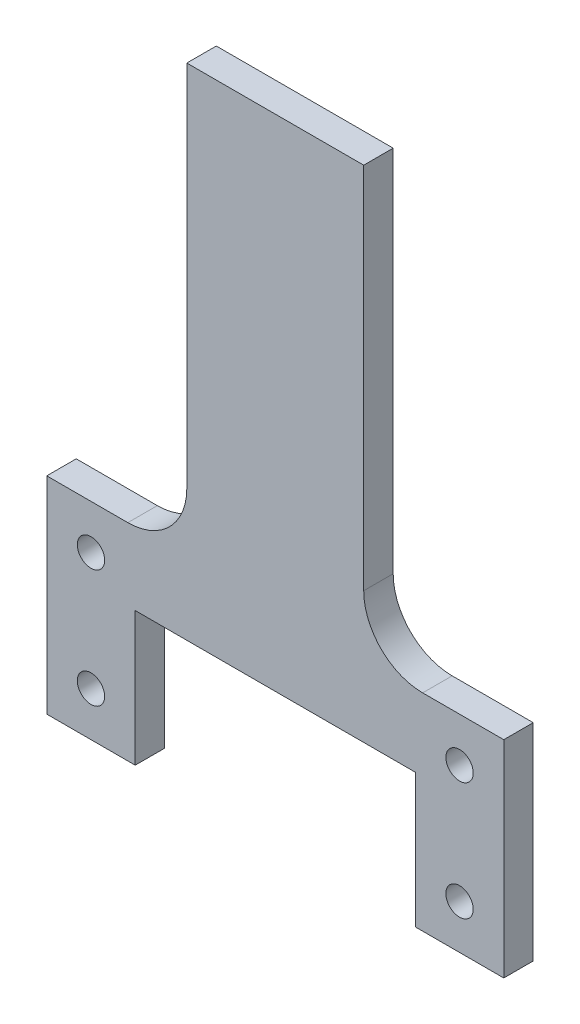
SolidWorks part; units mm, degrees
ref_plane "Front Plane" through (0, 0, 0) normal (0, 0, 1) x (1, 0, 0)
ref_plane "Top Plane" through (0, 0, 0) normal (0, 1, 0) x (1, 0, 0)
ref_plane "Right Plane" through (0, 0, 0) normal (1, 0, 0) x (0, 0, -1)
sketch "Sketch1" plane through (0, 0, 0) normal (0, 0, 1) x (1, 0, 0)
  line L0 (0, 0) -> (0, -21.6729) construction
  line L1 (-15.0812, -10.9093) -> (15.0813, -10.9093) construction
  line L2 (-15.0813, 3.3878) -> (-15.0812, -10.9093) construction
  line L3 (-15.0813, -3.0353) -> (-15.0812, -17.4625)
  line L4 (-15.0812, -17.4625) -> (-24.6062, -17.4625)
  line L5 (-24.6062, -17.4625) -> (-24.6062, 4.7625)
  line L6 (-15.0813, -3.0353) -> (15.0813, -3.0353)
  line L7 (-24.6062, 4.7625) -> (-9.525, 4.7625)
  line L8 (-9.525, 4.7625) -> (-9.525, 50.8)
  line L9 (-9.525, 50.8) -> (9.525, 50.8)
  line L10 (15.0813, 3.3878) -> (15.0813, -10.9093) construction
  line L11 (9.525, 4.7625) -> (9.525, 50.8)
  line L12 (24.6062, 4.7625) -> (9.525, 4.7625)
  line L13 (24.6063, -17.4625) -> (24.6062, 4.7625)
  line L14 (15.0813, -17.4625) -> (24.6063, -17.4625)
  line L15 (15.0813, -3.0353) -> (15.0813, -17.4625)
  circle A0 centre (-19.8438, 0) radius 1.9812 construction
  circle A1 centre (-19.8438, -12.7) radius 1.9812 construction
  circle A2 centre (19.8438, -12.7) radius 1.9812 construction
  circle A3 centre (19.8438, 0) radius 1.9812 construction
  circle A4 centre (19.8438, -12.7) radius 1.9812 construction
  circle A5 centre (19.8438, 0) radius 1.9812 construction
  point P26 (0, -10.9093)
  point P27 (0, 50.8)
  point P30 (0, -3.0353)
  dimension "D1" = 3.9624
  dimension "D2" = 12.7
  dimension "D3" = 39.6875
  dimension "D4" = 10.9093
  dimension "D5" = 4.7625
  dimension "D6" = 7.874
  dimension "D7" = 4.7625
  dimension "D8" = 4.7625
  dimension "D9" = 19.05
  dimension "D10" = 50.8
  dimension "D11" = 4.7625
extrude "Boss-Extrude1" add sketch "Sketch1" along normal blind 3.175
hole_wizard "#4 Clearance Hole1" positions "Sketch3" profile "Sketch2" hole size "#4" standard "ANSI Inch"
sketch "Sketch3" plane through (0, 0, 3.175) normal (0, 0, 1) x (1, 0, 0)
  point P0 (-19.8438, 0)
  point P3 (19.8438, 0)
  point P6 (19.8438, -12.7)
  point P9 (-19.8438, -12.7)
sketch "Sketch2" plane through (-19.8438, 0, 3.175) normal (1, 0, 0) x (0, -1, 0)
  line L0 (0, 0) -> (0, 4.1872)
  line L1 (0, 4.1872) -> (1.4732, 3.302)
  line L2 (1.4732, 3.302) -> (1.4732, 0)
  line L5 (1.4732, 0) -> (0, 0)
  line L10 (0, 4.1872) -> (-1.4732, 3.302) construction
  line L11 (0, -6.35) -> (0, 107.95) construction
  dimension "Hole Dia." = 2.9464
  dimension "Hole Depth" = 3.302
  dimension "Drill Angle" = 118
fillet "Fillet1" radius 6.35 2 edges at (9.525, 4.7625, 1.5875) (-9.525, 4.7625, 1.5875)
